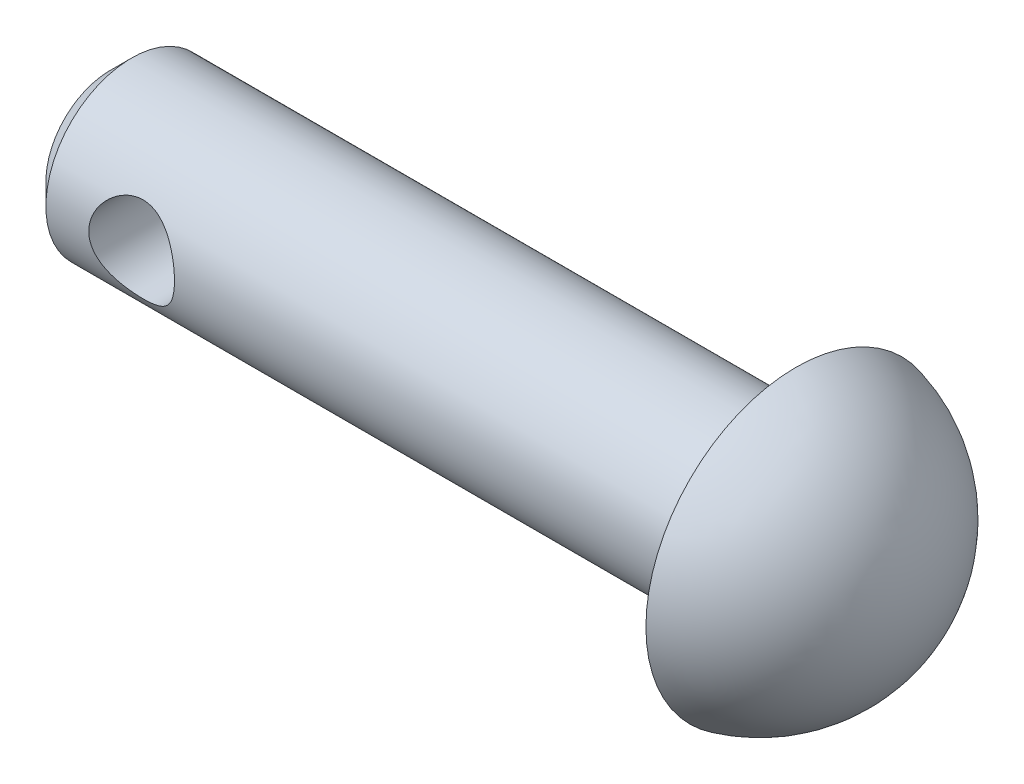
SolidWorks part; units mm, degrees
ref_plane "Front Plane" through (0, 0, 0) normal (0, 0, 1) x (1, 0, 0)
ref_plane "Top Plane" through (0, 0, 0) normal (0, 1, 0) x (1, 0, 0)
ref_plane "Right Plane" through (0, 0, 0) normal (1, 0, 0) x (0, 0, -1)
sketch "Sketch1" plane through (0, 0, 0) normal (1, 0, 0) x (0, 0, -1)
  circle A0 centre (0, 0) radius 2
  dimension "D1" = 4
extrude "Boss-Extrude1" add sketch "Sketch1" against normal blind 16
sketch "Sketch2" plane through (0, 0, 0) normal (0, 0, 1) x (1, 0, 0)
  line L0 (-16, 2) -> (-16, -2) construction
  circle A0 centre (-13.5, 0) radius 1
  dimension "D1" = 2
  dimension "D2" = 2.5
extrude "Cut-Extrude1" cut sketch "Sketch2" against normal through all both and the other way through all
sketch "Sketch3" plane through (0, 0, 0) normal (0, 1, 0) x (1, 0, 0)
  line L0 (-5.0978, 0) -> (5.0691, 0) construction
  line L1 (2.7574, 0) -> (0, 0)
  line L2 (0, 0) -> (0, 3.5)
  arc A0 (0, 3.5) -> (2.7574, 0) centre (-0.8426, 0) cw
  dimension "D2" = 3.6
  dimension "D1" = 3.5
revolve "Revolve1" add sketch "Sketch3" angle 360 about L0
chamfer "Chamfer1" distance 0.5 angle 45 1 edges at (-16, 0, -2)
